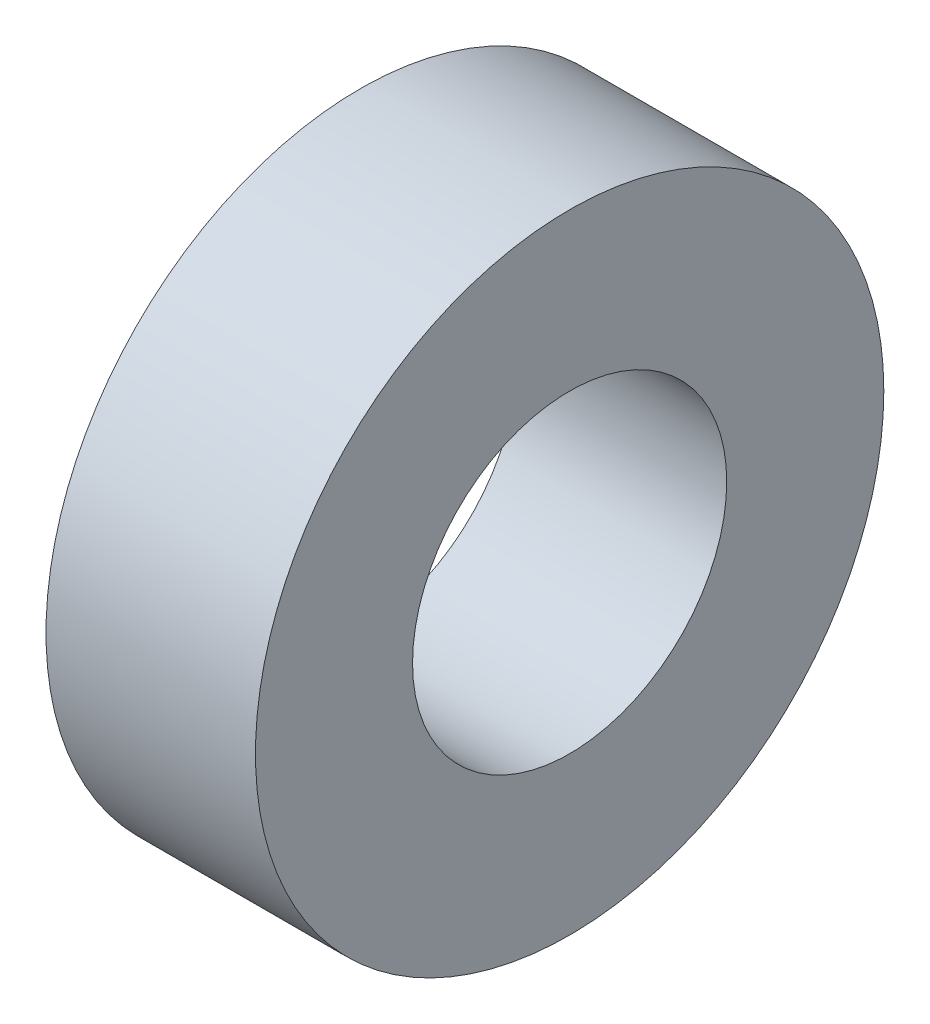
SolidWorks part; units mm, degrees
ref_plane "Front" through (0, 0, 0) normal (0, 0, 1) x (1, 0, 0)
ref_plane "Top" through (0, 0, 0) normal (0, 1, 0) x (1, 0, 0)
ref_plane "Right" through (0, 0, 0) normal (1, 0, 0) x (0, 0, -1)
sketch "草图1" plane through (0, 0, 0) normal (1, 0, 0) x (0, 0, -1)
  circle A0 centre (0, 0) radius 6
  circle A1 centre (0, 0) radius 3
  dimension "D1" = 12
  dimension "D2" = 6
extrude "凸台-拉伸1" add sketch "草图1" along normal blind 4
